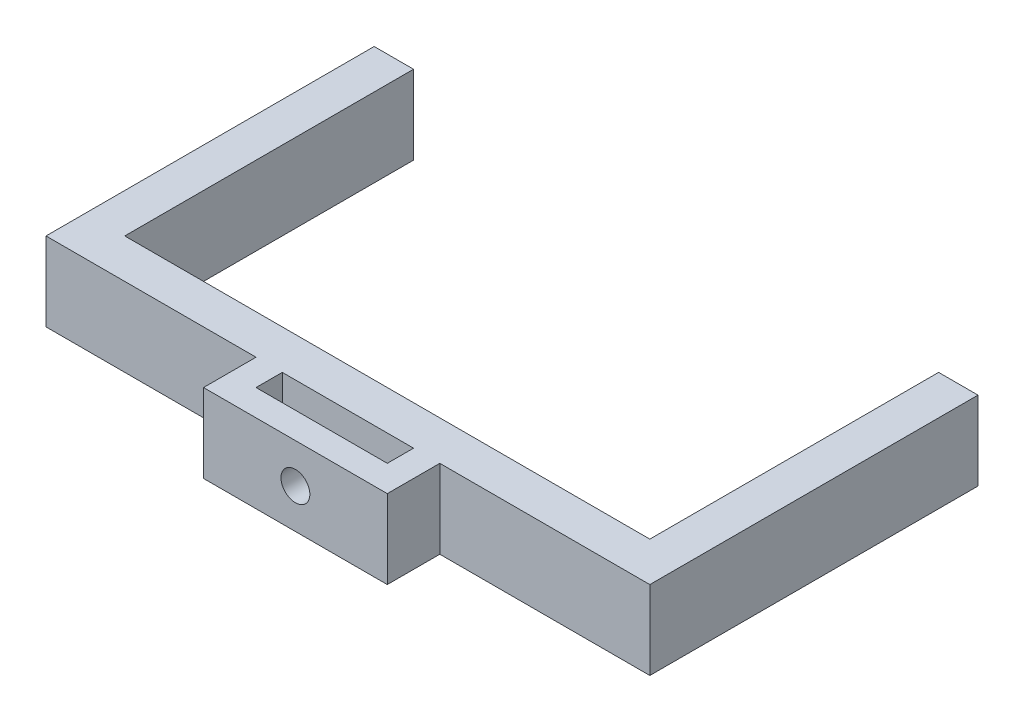
SolidWorks part; units mm, degrees
ref_plane "前视基准面" through (0, 0, 0) normal (0, 0, 1) x (1, 0, 0)
ref_plane "上视基准面" through (0, 0, 0) normal (0, 1, 0) x (1, 0, 0)
ref_plane "右视基准面" through (0, 0, 0) normal (1, 0, 0) x (0, 0, -1)
other "Configuration Table"
sketch "Sketch1" plane through (0, 0, 0) normal (0, 1, 0) x (1, 0, 0)
  line L0 (20, 0) -> (20, -3.2739)
  line L1 (0, 0) -> (40, 0)
  line L2 (0, 0) -> (0, 3)
  line L3 (0, 3) -> (40, 3)
  line L4 (40, 0) -> (40, 3)
  line L5 (0, 0) -> (-3, 0)
  line L6 (0, 0) -> (0, 25)
  line L7 (0, 25) -> (-3, 25)
  line L8 (-3, 0) -> (-3, 25)
  line L9 (40, 0) -> (43, 0)
  line L10 (40, 0) -> (40, 25)
  line L11 (40, 25) -> (43, 25)
  line L12 (43, 0) -> (43, 25)
  line L14 (15, -4) -> (25, -4)
  line L15 (15, -4) -> (15, -2)
  line L16 (15, -2) -> (25, -2)
  line L17 (25, -4) -> (25, -2)
  line L18 (15, -4) -> (13, -4)
  line L19 (15, -4) -> (15, 0)
  line L20 (15, 0) -> (13, 0)
  line L21 (13, -4) -> (13, 0)
  line L22 (25, -4) -> (27, -4)
  line L23 (25, -4) -> (25, 0)
  line L24 (25, 0) -> (27, 0)
  line L25 (27, -4) -> (27, 0)
  dimension "D1" = 40
  dimension "D2" = 3
  dimension "D3" = 25
  dimension "D4" = 25
  dimension "D5" = 3
  dimension "D6" = 3
  dimension "D7" = 10
  dimension "D8" = 5
  dimension "D9" = 2
  dimension "D10" = 2
  dimension "D11" = 2
  dimension "D12" = 2
extrude "Boss-Extrude1" add sketch "Sketch1" along normal blind 6
sketch "Sketch2" plane through (0, 0, 4) normal (0, 0, 1) x (1, 0, 0)
  line L0 (20, 6) -> (20, 0)
  line L1 (27, 6) -> (13, 6) construction
  line L2 (27, 0) -> (13, 0) construction
  circle A0 centre (20, 3) radius 1.1
  dimension "D1" = 2.2
extrude "Cut-Extrude1" cut sketch "Sketch2" against normal blind 2 contours A0
